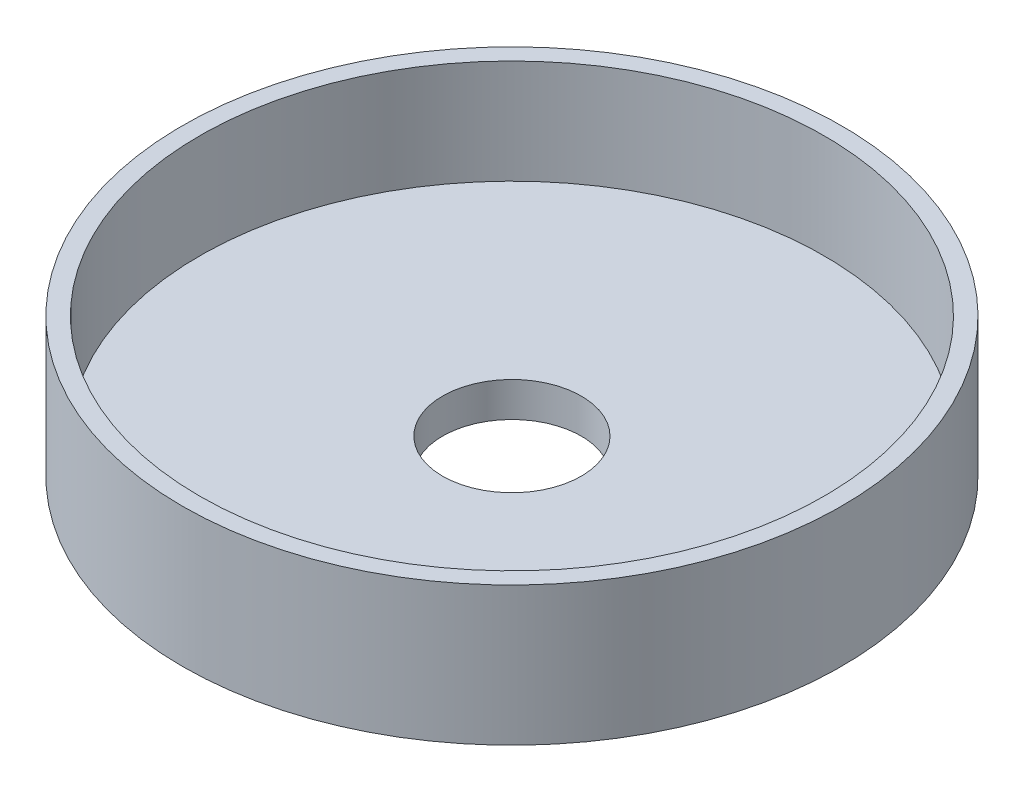
SolidWorks part; units mm, degrees
ref_plane "Front Plane" through (0, 0, 0) normal (0, 0, 1) x (1, 0, 0)
ref_plane "Top Plane" through (0, 0, 0) normal (0, 1, 0) x (1, 0, 0)
ref_plane "Right Plane" through (0, 0, 0) normal (1, 0, 0) x (0, 0, -1)
sketch "Sketch1" plane through (0, 0, 0) normal (0, 1, 0) x (1, 0, 0)
  circle A0 centre (0, 0) radius 23.75
  dimension "D1" = 47.5
extrude "Boss-Extrude1" add sketch "Sketch1" along normal blind 10
sketch "Sketch2" plane through (0, 10, 0) normal (0, 1, 0) x (1, 0, 0)
  circle A0 centre (0, 0) radius 22.5
  dimension "D1" = 45
extrude "Cut-Extrude1" cut sketch "Sketch2" against normal blind 7.5
sketch "Sketch3" plane through (0, 2.5, 0) normal (0, 1, 0) x (1, 0, 0)
  circle A0 centre (0, 0) radius 5
  dimension "D1" = 10
extrude "Cut-Extrude2" cut sketch "Sketch3" against normal blind 7.5
